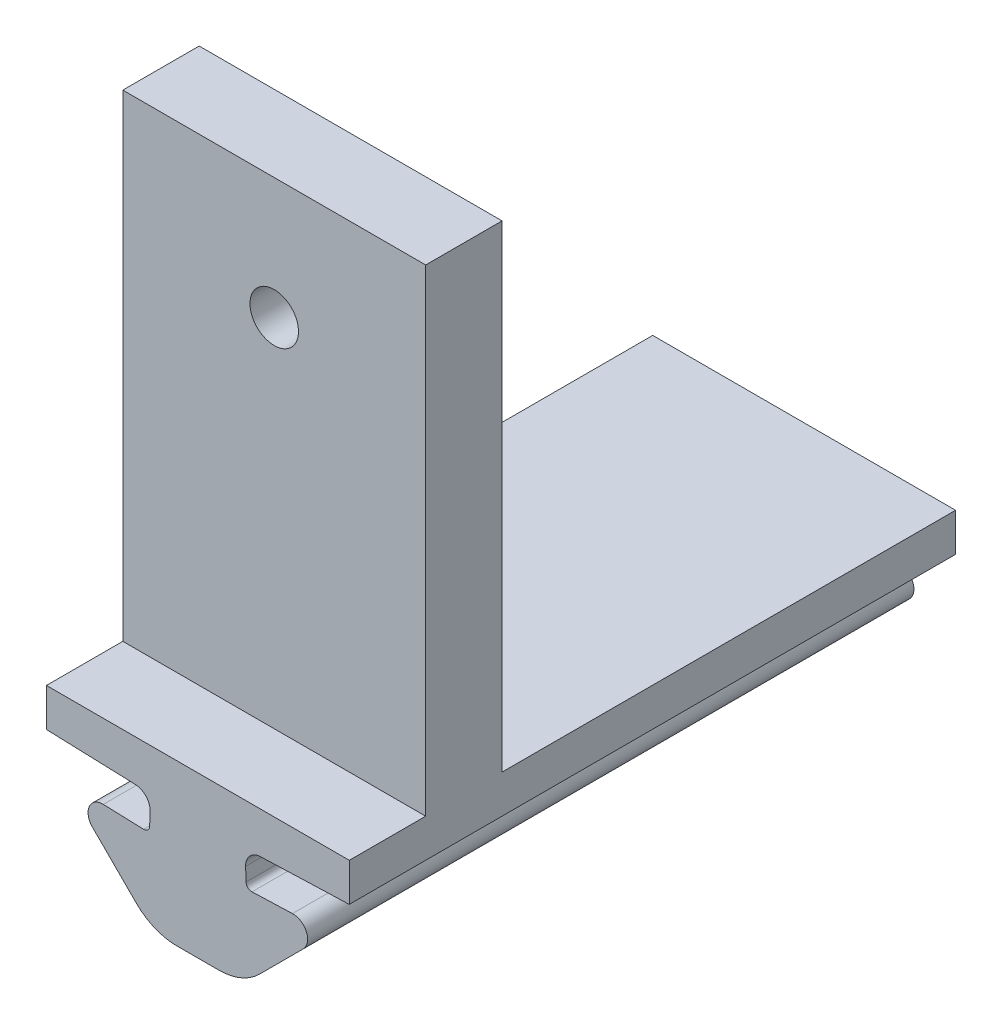
SolidWorks part; units mm, degrees
ref_plane "Front Plane" through (0, 0, 0) normal (0, 0, 1) x (1, 0, 0)
ref_plane "Top Plane" through (0, 0, 0) normal (0, 1, 0) x (1, 0, 0)
ref_plane "Right Plane" through (0, 0, 0) normal (1, 0, 0) x (0, 0, -1)
sketch "Sketch2" plane through (0, 0, 0) normal (0, 0, 1) x (1, 0, 0)
  line L1 (-50.3756, 45.6099) -> (-50.3512, 46.3094)
  line L2 (-50.6859, 45.3205) -> (-52.8037, 45.3945)
  line L6 (-55.7809, 47.2995) -> (-51.1228, 47.1369)
  line L7 (-51.0743, 41.7794) -> (-53.3751, 44.0803)
  line L8 (-47.8507, 40.9008) -> (-48.9529, 40.9008)
  line L9 (-47.8507, 40.9008) -> (-47.8507, 47.2995)
  line L10 (-47.8507, 47.2995) -> (-55.7809, 47.2995)
  arc A0 (-50.6859, 45.3205) -> (-50.3756, 45.6099) centre (-50.6754, 45.6203) ccw
  arc A7 (-50.3512, 46.3094) -> (-51.1228, 47.1369) centre (-51.1507, 46.3374) ccw
  arc A8 (-52.8037, 45.3945) -> (-53.3751, 44.0803) centre (-52.8306, 44.6248) ccw
  arc A9 (-51.0743, 41.7794) -> (-48.9529, 40.9008) centre (-48.9529, 43.9008) ccw
extrude "Boss-Extrude1" add sketch "Sketch2" along normal blind 31.75
ref_plane "Plane2" through (0, 0, 0) normal (0.7071, -0.7071, 0) x (-0.7071, -0.7071, 0)
ref_plane "Plane3" through (-42.746, 42.746, 0) normal (0.7071, -0.7071, 0) x (-0.7071, -0.7071, 0)
mirror "Mirror2" about plane through (-47.8507, 40.9008, 31.75) normal (-1, 0, 0) of "Boss-Extrude1"
ref_plane "Plane7" through (0, 47.2995, 0) normal (0, 1, 0) x (1, 0, 0)
sketch "Sketch19" plane through (0, 47.2995, 0) normal (0, 1, 0) x (1, 0, 0)
  line L0 (-55.7809, -31.75) -> (-55.7809, 0) construction
  line L1 (-55.7809, 0) -> (-39.9205, 0)
  line L2 (-55.7809, 0) -> (-55.7809, -31.75)
  line L3 (-55.7809, -31.75) -> (-39.9205, -31.75)
  line L4 (-39.9205, 0) -> (-39.9205, -31.75)
  line L5 (-39.9205, -31.75) -> (-39.9205, 0) construction
  line L6 (-39.9205, 0) -> (-55.7809, 0) construction
  dimension "D1" = 0
  dimension "D2" = 31.75
extrude "Boss-Extrude7" add sketch "Sketch19" along normal blind 2
sketch "Sketch23" plane through (0, 49.2995, 0) normal (0, 1, 0) x (1, 0, 0)
  line L0 (-55.7809, 0) -> (-55.7809, -31.75) construction
  line L1 (-55.7809, -23.75) -> (-39.9205, -23.75)
  line L2 (-55.7809, -23.75) -> (-55.7809, -27.75)
  line L3 (-55.7809, -27.75) -> (-39.9205, -27.75)
  line L4 (-39.9205, -23.75) -> (-39.9205, -27.75)
  line L5 (-39.9205, -31.75) -> (-39.9205, 0) construction
  line L6 (-39.9205, 0) -> (-55.7809, 0) construction
  dimension "D1" = 4
  dimension "D2" = 0
  dimension "D3" = 0
  dimension "D4" = 27.75
extrude "Boss-Extrude8" add sketch "Sketch23" along normal blind 25
ref_plane "Plane8" through (-39.9205, 49.2995, 23.75) normal (0, -1, 0) x (-1, 0, 0)
sketch "Sketch24" plane through (0, 0, 23.75) normal (0, 0, -1) x (-1, 0, 0)
  line L0 (39.9205, 74.2995) -> (55.7809, 74.2995) construction
  line L2 (47.8507, 74.2995) -> (47.8507, 61.5995) construction
  circle A1 centre (47.8507, 67.9495) radius 1.27
  dimension "D4" = 2.54
  dimension "D5" = 6.35
extrude "Cut-Extrude1" cut sketch "Sketch24" against normal through all
